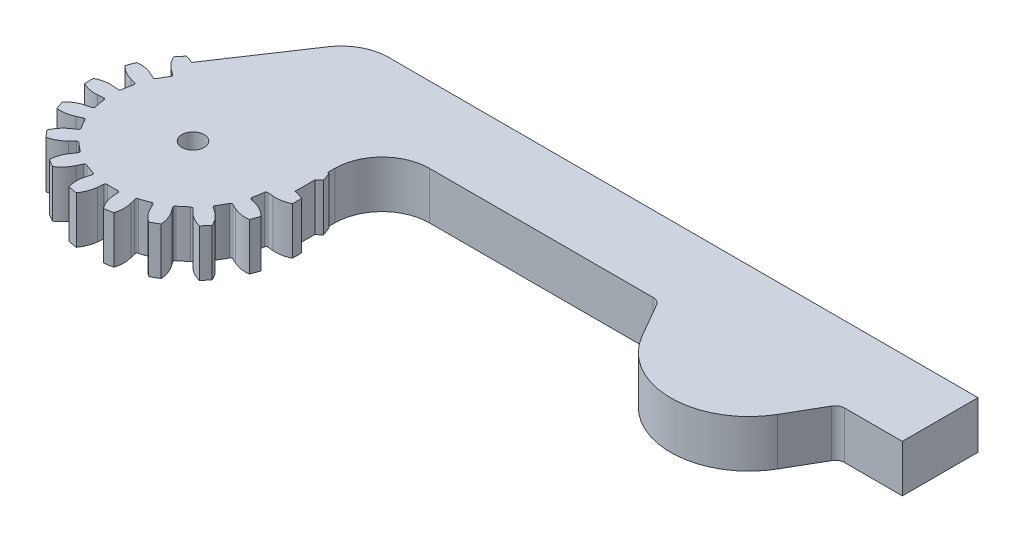
SolidWorks part; units mm, degrees
ref_plane "Front Plane" through (0, 0, 0) normal (0, 0, 1) x (1, 0, 0)
ref_plane "Top Plane" through (0, 0, 0) normal (0, 1, 0) x (1, 0, 0)
ref_plane "Right Plane" through (0, 0, 0) normal (1, 0, 0) x (0, 0, -1)
sketch "Sketch1" plane through (0, 0, 0) normal (0, 1, 0) x (1, 0, 0)
  line L0 (0, 0) -> (0, 13.97) construction
  line L1 (0, 0) -> (-2.4259, 13.7578) construction
  line L2 (0, 0) -> (-3.0237, 13.6389) construction
  line L3 (0, 0) -> (-3.0578, 11.4119) construction
  line L4 (-2.8672, 10.7004) -> (-3.0578, 11.4119)
  line L5 (0, 0) -> (-3.703, 10.1738) construction
  line L6 (-3.703, 10.1738) -> (0, 0)
  line L7 (-0.9655, 11.0357) -> (-1.0297, 11.7695)
  line L8 (0, 10.8267) -> (0, 0)
  circle A0 centre (0, 0) radius 13.97 construction
  circle A1 centre (0, 0) radius 11.8144 construction
  circle A2 centre (0, 0) radius 10.8268 construction
  arc A3 (-3.0237, 13.6389) -> (-2.4259, 13.7578) centre (0, 0) cw
  arc A4 (-3.703, 10.1738) -> (-3.0412, 10.3909) centre (0, 0) cw
  arc A5 (-3.0578, 11.4119) -> (-3.0237, 13.6389) centre (0.8739, 12.4654) cw
  arc A6 (-3.0412, 10.3909) -> (-2.8672, 10.7004) centre (-3.1125, 10.6346) ccw
  arc A7 (-1.8235, 13.8505) -> (-2.4259, 13.7578) centre (0, 0) ccw
  arc A8 (-1.0297, 11.7695) -> (-1.8235, 13.8505) centre (-5.0846, 11.4147) ccw
  arc A9 (-0.6961, 10.8043) -> (-0.9655, 11.0357) centre (-0.7125, 11.0578) cw
  arc A10 (0, 10.8267) -> (-0.6961, 10.8043) centre (0, 0) ccw
  point P15 (-2.8022, 10.4578)
  dimension "D1" = 27.94
  dimension "D2" = 23.6289
  dimension "D3" = 3.1433
  dimension "D8" = 0.254
  dimension "D4" = 10
  dimension "D5" = 10
  dimension "D6" = 5
  dimension "D7" = 2.5
extrude "Boss-Extrude1" add sketch "Sketch1" along normal blind 6.35 contours L8 A10 A9 L7 A8 A7 A3 A5 L4 A6 A4 L6
pattern_circular "CirPattern1" count 18 every 20 about axis through (0, 0, 0) along (0, 1, 0) of "Boss-Extrude1"
sketch "Sketch2" plane through (0, 6.35, 0) normal (0, 1, 0) x (1, 0, 0)
  line L0 (57.15, 12.7) -> (57.15, 0) construction
  line L1 (19.05, 12.7) -> (49.0844, 12.7)
  line L2 (0, 12.7) -> (0, 22.86) construction
  line L3 (3.3942, 22.86) -> (57.15, 22.86)
  line L4 (57.15, 12.7) -> (57.15, 22.86) construction
  line L5 (-1.8857, 20.0378) -> (-10.5598, 7.0556)
  line L6 (12.7, 0) -> (12.7, 6.35)
  line L7 (56.93, 0.381) -> (50.1843, 12.065)
  line L8 (57.37, 0.381) -> (64.4823, 12.7)
  line L9 (68.1485, 22.86) -> (57.15, 22.86)
  line L10 (0, 0) -> (12.7, 0)
  line L11 (0, 0) -> (-10.3509, 7.3682)
  line L12 (57.15, 22.86) -> (82.55, 22.86)
  line L13 (82.55, 22.86) -> (82.55, 12.7)
  line L14 (49.0844, 12.7) -> (49.8177, 12.7)
  line L15 (74.8024, 12.7) -> (83.656, 12.7)
  line L16 (73.7025, 12.065) -> (66.7368, 0)
  line L17 (50.1843, 12.065) -> (49.5567, 13.152)
  line L18 (49.8177, 12.7) -> (74.0692, 12.7)
  circle A0 centre (0, 0) radius 12.7 construction
  arc A1 (57.37, 0.381) -> (56.93, 0.381) centre (57.15, 0.508) cw
  arc A2 (68.1485, 22.86) -> (69.2484, 20.955) centre (68.1485, 21.59) cw
  arc A3 (3.3942, 22.86) -> (-1.8857, 20.0378) centre (3.3942, 16.51) ccw
  arc A4 (19.05, 12.7) -> (12.7, 6.35) centre (19.05, 6.35) ccw
  arc A5 (49.0844, 12.7) -> (50.1843, 12.065) centre (49.0844, 11.43) cw
  arc A6 (-11.0831, 8.5044) -> (-9.6778, 6.7765) centre (-7.3431, 10.1107) ccw construction
  arc A7 (52.8491, 7.4494) -> (71.0377, 7.4494) centre (61.9434, 12.7) ccw
  arc A8 (73.7025, 12.065) -> (74.8024, 12.7) centre (74.8024, 11.43) cw
  point P2 (64.4823, 12.7)
  dimension "D1" = 25.4
  dimension "D6" = 0.254
  dimension "D7" = 1.27
  dimension "D8" = 6.35
  dimension "D2" = 6.35
  dimension "D9" = 1.27
  dimension "D13" = 1.27
  dimension "D3" = 57.15
  dimension "D4" = 30
  dimension "D5" = 30
  dimension "D10" = 10.16
  dimension "D11" = 3.3942
  dimension "D12" = 25.4
sketch "Sketch3" plane through (0, 6.35, 0) normal (0, 1, 0) x (1, 0, 0)
  circle A0 centre (0, 0) radius 1.5
  dimension "D1" = 3
extrude "Boss-Extrude2" add sketch "Sketch2" along normal blind 6.35 from surface at -6.35 starting at plane "Top Plane"
extrude "Cut-Extrude1" cut sketch "Sketch3" against normal blind 6.35
